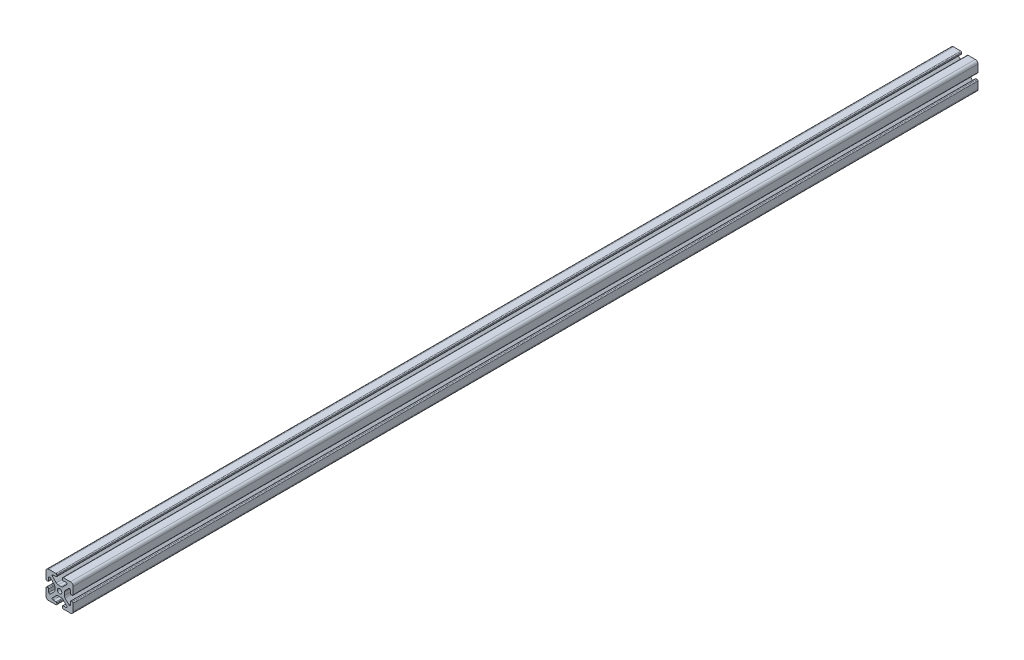
SolidWorks part; units mm, degrees
material "3003 Alloy"
ref_plane "Front Plane" through (0, 0, 0) normal (0, 0, 1) x (1, 0, 0)
ref_plane "Top Plane" through (0, 0, 0) normal (0, 1, 0) x (1, 0, 0)
ref_plane "Right Plane" through (0, 0, 0) normal (1, 0, 0) x (0, 0, -1)
sketch "Sketch1" plane through (0, 0, 0) normal (0, 0, 1) x (1, 0, 0)
  line B0 (1.6032, 5.25) -> (-1.6032, 5.25)
  arc B1 (-12, 15) -> (-15, 12) centre (-12, 12) ccw
  line B2 (-7.1276, 12) -> (-3.9, 12)
  line B3 (7.8506, 10.2547) -> (3.7245, 6.1287)
  line B4 (-10.2547, 7.8506) -> (-6.1287, 3.7245)
  line B5 (3.1, -12.8) -> (3.1, -14)
  arc B6 (3.9, -12) -> (3.1, -12.8) centre (3.9, -12.8) ccw
  line B7 (7.1276, -12) -> (3.9, -12)
  arc B8 (7.1276, -12) -> (7.8506, -10.2547) centre (7.1276, -10.9776) ccw
  line B9 (3.7245, -6.1287) -> (7.8506, -10.2547)
  arc B10 (3.7245, -6.1287) -> (1.6032, -5.25) centre (1.6032, -8.25) ccw
  line B11 (-1.6032, -5.25) -> (1.6032, -5.25)
  arc B12 (-1.6032, -5.25) -> (-3.7245, -6.1287) centre (-1.6032, -8.25) ccw
  line B13 (-7.8506, -10.2547) -> (-3.7245, -6.1287)
  arc B14 (-7.8506, -10.2547) -> (-7.1276, -12) centre (-7.1276, -10.9776) ccw
  line B15 (-3.9, -12) -> (-7.1276, -12)
  arc B16 (-3.1, -12.8) -> (-3.9, -12) centre (-3.9, -12.8) ccw
  line B17 (-3.1, -14) -> (-3.1, -12.8)
  arc B18 (-4.1, -15) -> (-3.1, -14) centre (-4.1, -14) ccw
  line B19 (-12, -15) -> (-4.1, -15)
  arc B20 (-15, -12) -> (-12, -15) centre (-12, -12) ccw
  line B21 (-15, -4.1) -> (-15, -12)
  arc B22 (-14, -3.1) -> (-15, -4.1) centre (-14, -4.1) ccw
  line B23 (-12.8, -3.1) -> (-14, -3.1)
  arc B24 (-12, -3.9) -> (-12.8, -3.1) centre (-12.8, -3.9) ccw
  line B25 (-12, -7.1276) -> (-12, -3.9)
  arc B26 (-12, -7.1276) -> (-10.2547, -7.8506) centre (-10.9776, -7.1276) ccw
  line B27 (-6.1287, -3.7245) -> (-10.2547, -7.8506)
  arc B28 (-6.1287, -3.7245) -> (-5.25, -1.6032) centre (-8.25, -1.6032) ccw
  line B29 (-5.25, 1.6032) -> (-5.25, -1.6032)
  arc B30 (-5.25, 1.6032) -> (-6.1287, 3.7245) centre (-8.25, 1.6032) ccw
  arc B31 (-10.2547, 7.8506) -> (-12, 7.1276) centre (-10.9776, 7.1276) ccw
  line B32 (-12, 3.9) -> (-12, 7.1276)
  arc B33 (-12.8, 3.1) -> (-12, 3.9) centre (-12.8, 3.9) ccw
  line B34 (-14, 3.1) -> (-12.8, 3.1)
  arc B35 (-15, 4.1) -> (-14, 3.1) centre (-14, 4.1) ccw
  line B36 (-15, 12) -> (-15, 4.1)
  line B37 (-4.1, 15) -> (-12, 15)
  arc B38 (-3.1, 14) -> (-4.1, 15) centre (-4.1, 14) ccw
  line B39 (-3.1, 12.8) -> (-3.1, 14)
  arc B40 (-3.9, 12) -> (-3.1, 12.8) centre (-3.9, 12.8) ccw
  arc B41 (-7.1276, 12) -> (-7.8506, 10.2547) centre (-7.1276, 10.9776) ccw
  line B42 (-3.7245, 6.1287) -> (-7.8506, 10.2547)
  arc B43 (-3.7245, 6.1287) -> (-1.6032, 5.25) centre (-1.6032, 8.25) ccw
  arc B44 (1.6032, 5.25) -> (3.7245, 6.1287) centre (1.6032, 8.25) ccw
  arc B45 (7.8506, 10.2547) -> (7.1276, 12) centre (7.1276, 10.9776) ccw
  line B46 (3.9, 12) -> (7.1276, 12)
  arc B47 (3.1, 12.8) -> (3.9, 12) centre (3.9, 12.8) ccw
  line B48 (3.1, 14) -> (3.1, 12.8)
  arc B49 (4.1, 15) -> (3.1, 14) centre (4.1, 14) ccw
  line B50 (12, 15) -> (4.1, 15)
  arc B51 (15, 12) -> (12, 15) centre (12, 12) ccw
  line B52 (15, 4.1) -> (15, 12)
  arc B53 (14, 3.1) -> (15, 4.1) centre (14, 4.1) ccw
  line B54 (12.8, 3.1) -> (14, 3.1)
  arc B55 (12, 3.9) -> (12.8, 3.1) centre (12.8, 3.9) ccw
  line B56 (12, 7.1276) -> (12, 3.9)
  arc B57 (12, 7.1276) -> (10.2547, 7.8506) centre (10.9776, 7.1276) ccw
  line B58 (6.1287, 3.7245) -> (10.2547, 7.8506)
  arc B59 (6.1287, 3.7245) -> (5.25, 1.6032) centre (8.25, 1.6032) ccw
  line B60 (5.25, -1.6032) -> (5.25, 1.6032)
  arc B61 (5.25, -1.6032) -> (6.1287, -3.7245) centre (8.25, -1.6032) ccw
  line B62 (10.2547, -7.8506) -> (6.1287, -3.7245)
  arc B63 (10.2547, -7.8506) -> (12, -7.1276) centre (10.9776, -7.1276) ccw
  line B64 (12, -3.9) -> (12, -7.1276)
  arc B65 (12.8, -3.1) -> (12, -3.9) centre (12.8, -3.9) ccw
  line B66 (14, -3.1) -> (12.8, -3.1)
  arc B67 (15, -4.1) -> (14, -3.1) centre (14, -4.1) ccw
  line B68 (15, -12) -> (15, -4.1)
  arc B69 (12, -15) -> (15, -12) centre (12, -12) ccw
  line B70 (4.1, -15) -> (12, -15)
  arc B71 (3.1, -14) -> (4.1, -15) centre (4.1, -14) ccw
  circle B72 centre (0, 0) radius 2.5
sketch_block_instance "IR 30X30 IR41901-2"
sketch_block "IR 30X30 IR41901"
extrude "Boss-Extrude1" add sketch "Sketch1" along normal blind 1000
